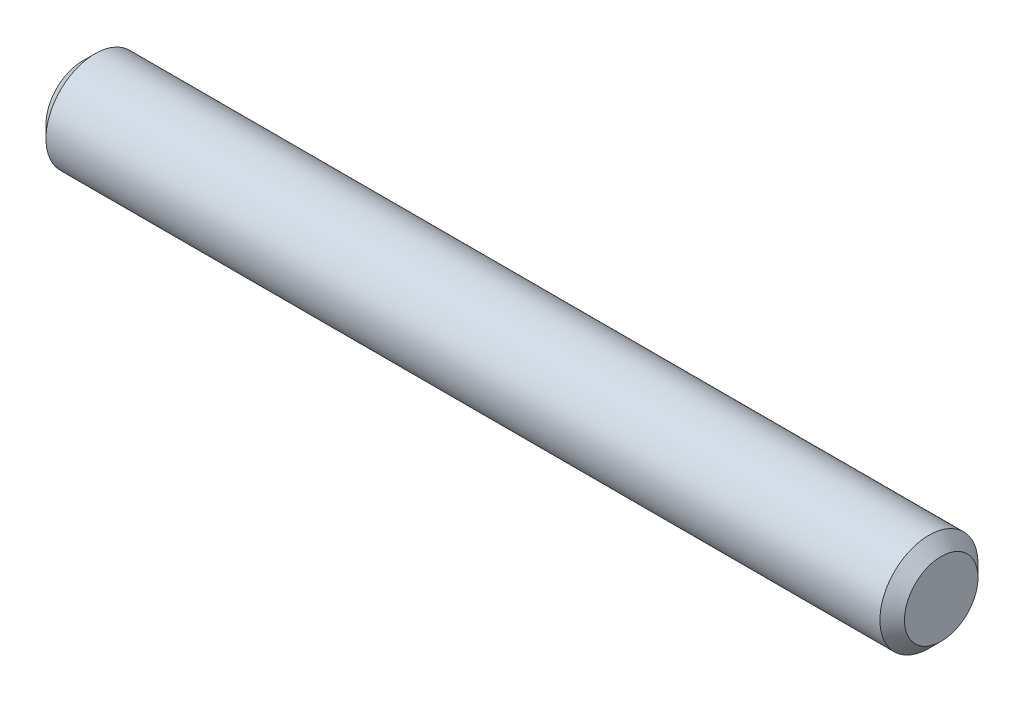
SolidWorks part; units mm, degrees
ref_plane "Ebene vorne" through (0, 0, 0) normal (0, 0, 1) x (1, 0, 0)
ref_plane "Ebene oben" through (0, 0, 0) normal (0, 1, 0) x (1, 0, 0)
ref_plane "Ebene rechts" through (0, 0, 0) normal (1, 0, 0) x (0, 0, -1)
sketch "Skizze1" plane through (0, 0, 0) normal (1, 0, 0) x (0, 0, -1)
  circle A0 centre (0, 0) radius 2
  dimension "D1" = 4
extrude "Aufsatz-Linear austragen1" add sketch "Skizze1" along normal mid plane 35
chamfer "Fase1" distance 0.5 angle 45 2 edges at (-17.5, 0, -2) (17.5, 0, -2)
